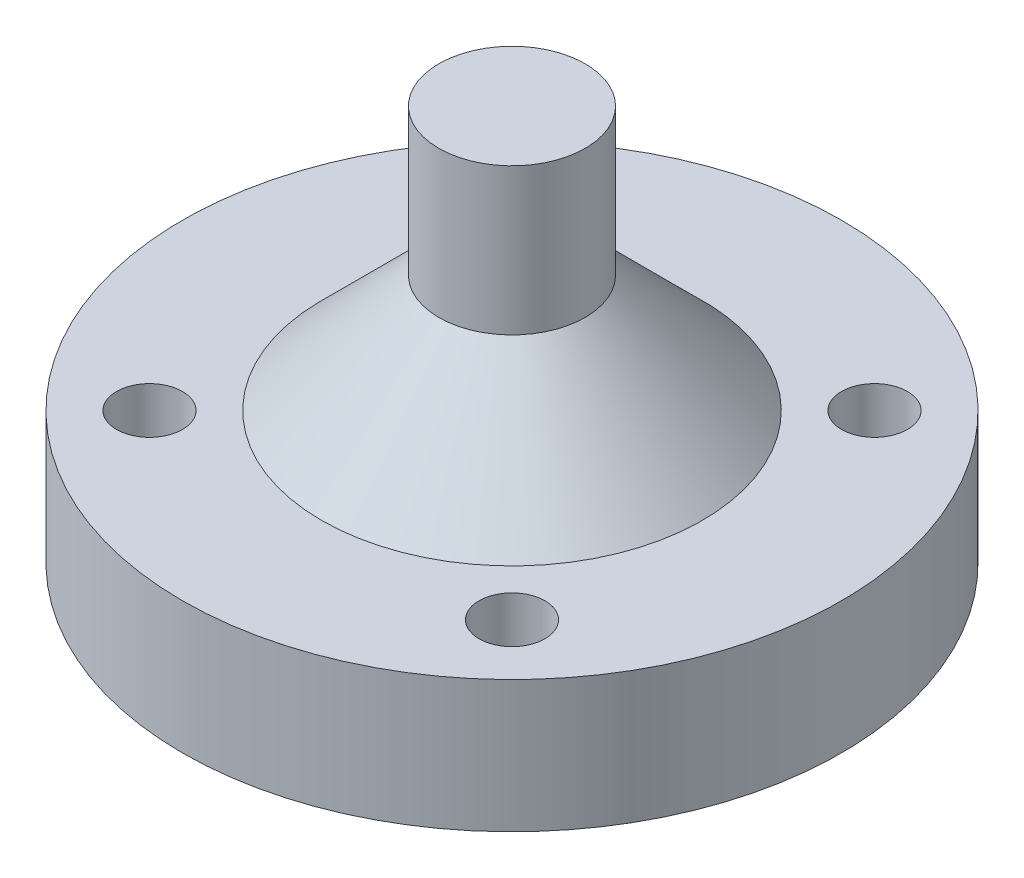
SolidWorks part; units mm, degrees
ref_plane "Front Plane" through (0, 0, 0) normal (0, 0, 1) x (1, 0, 0)
ref_plane "Top Plane" through (0, 0, 0) normal (0, 1, 0) x (1, 0, 0)
ref_plane "Right Plane" through (0, 0, 0) normal (1, 0, 0) x (0, 0, -1)
sketch "Sketch1" plane through (0, 0, 0) normal (0, 1, 0) x (1, 0, 0)
  circle A0 centre (0, 0) radius 22.5
  dimension "D1" = 45
extrude "Boss-Extrude1" add sketch "Sketch1" along normal blind 9
sketch "Sketch2" plane through (0, 9, 0) normal (0, 1, 0) x (1, 0, 0)
  line L0 (0, 0) -> (12.3744, 12.3744) construction
  circle A0 centre (0, 0) radius 17.5 construction
  circle A1 centre (12.3744, 12.3744) radius 2.25
  dimension "D1" = 35
  dimension "D2" = 4.5
extrude "Cut-Extrude1" cut sketch "Sketch2" against normal through all
pattern_circular "CirPattern1" count 4 over 360 about axis through (0, 0, 0) along (0, 1, 0) of "Cut-Extrude1"
sketch "Sketch3" plane through (0, 9, 0) normal (0, 1, 0) x (1, 0, 0)
  circle A0 centre (0, 0) radius 5
  dimension "D1" = 10
extrude "Boss-Extrude2" add sketch "Sketch3" along normal blind 18
chamfer "Chamfer1" distance 8 angle 45 1 edges at (0, 9, 5)
sketch "Sketch6" plane through (0, 0, 0) normal (0, -1, 0) x (1, 0, 0)
  circle A0 centre (0, 0) radius 10.75
  dimension "D1" = 21.5
extrude "Cut-Extrude4" cut sketch "Sketch6" against normal blind 6
